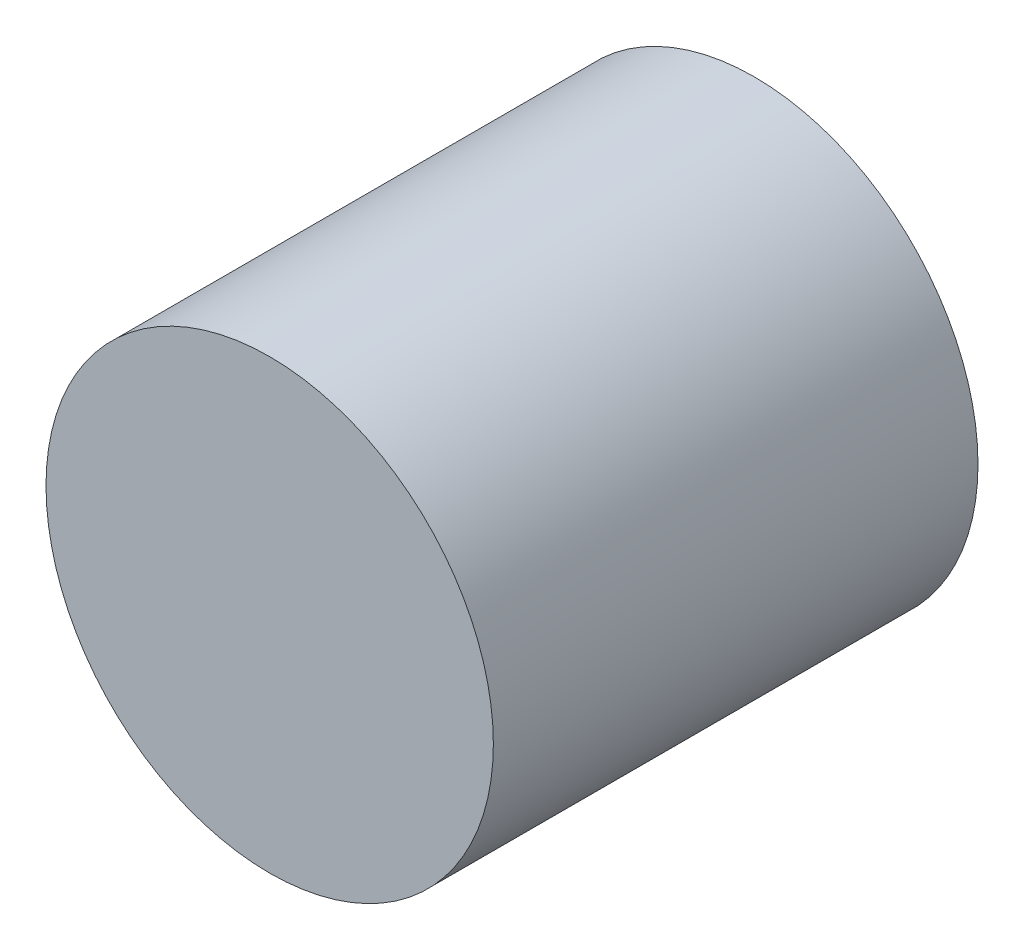
SolidWorks part; units mm, degrees
ref_plane "Front Plane" through (0, 0, 0) normal (0, 0, 1) x (1, 0, 0)
ref_plane "Top Plane" through (0, 0, 0) normal (0, 1, 0) x (1, 0, 0)
ref_plane "Right Plane" through (0, 0, 0) normal (1, 0, 0) x (0, 0, -1)
sketch "Sketch1" plane through (0, 0, 0) normal (0, 0, 1) x (1, 0, 0)
  circle A0 centre (0, 0) radius 3
extrude "Boss-Extrude1" add sketch "Sketch1" along normal blind 6.5
